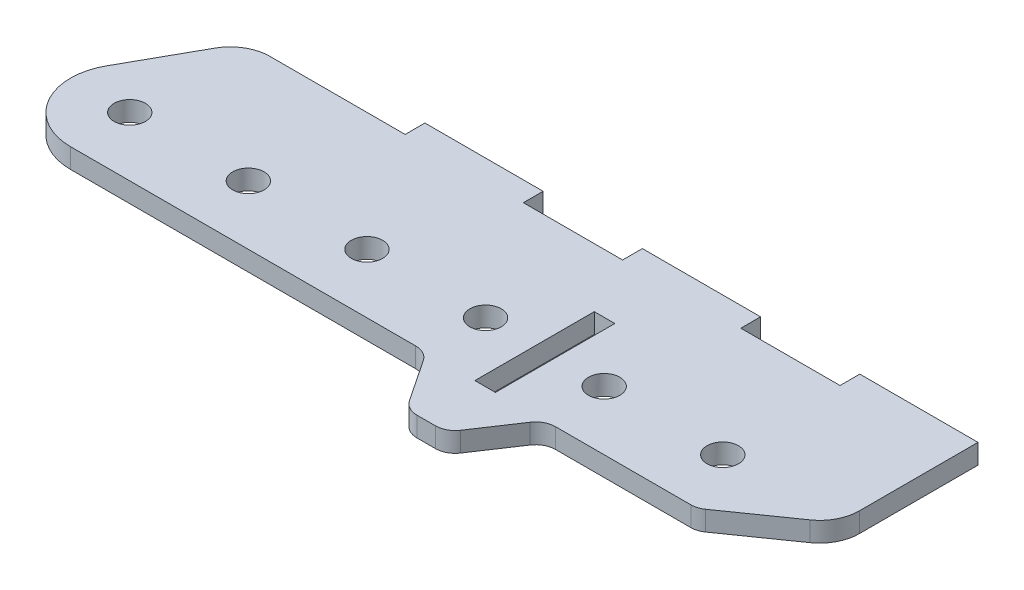
SolidWorks part; units mm, degrees
material "Plain Carbon Steel"
ref_plane "Front Plane" through (0, 0, 0) normal (0, 0, 1) x (1, 0, 0)
ref_plane "Top Plane" through (0, 0, 0) normal (0, 1, 0) x (1, 0, 0)
ref_plane "Right Plane" through (0, 0, 0) normal (1, 0, 0) x (0, 0, -1)
sketch "Sketch1" plane through (0, 0, 0) normal (0, 1, 0) x (1, 0, 0)
  line L1 (0, 0) -> (-304.8, 0)
  line L2 (0, 0) -> (0, -76.2)
  line L3 (0, -76.2) -> (-304.8, -76.2)
  line L4 (-304.8, 0) -> (-304.8, -76.2)
  dimension "D1" = 76.2
  dimension "D2" = 304.8
extrude "Boss-Extrude1" add sketch "Sketch1" along normal blind 6.35
chamfer "Chamfer1" distance 53.975 angle 35 1 edges at (0, 3.175, 76.2)
sketch "Sketch2" plane through (0, 6.35, 0) normal (0, 1, 0) x (1, 0, 0)
  line L0 (0, 0) -> (0, 6.35)
  line L1 (0, 6.35) -> (-37.973, 6.35)
  line L3 (-37.973, 6.35) -> (-37.973, 0)
  line L4 (0, 0) -> (-304.8, 0) construction
  line L5 (-37.973, 0) -> (0, 0)
  dimension "D1" = 37.973
  dimension "D2" = 6.35
extrude "Boss-Extrude2" add sketch "Sketch2" against normal blind 6.35
pattern_linear "LPattern1" count 3 spacing 69.85 along (-1, 0, 0) of "Boss-Extrude2"
hole_wizard "3/8 Clearance Hole1" positions "Sketch4" profile "Sketch5" hole size "3/8" standard "ANSI Inch" end condition through all
sketch "Sketch4" plane through (0, 6.35, 0) normal (0, 1, 0) x (1, 0, 0)
  point P0 (-37.5406, -38.1)
  point P3 (-75.6406, -38.1)
  point P6 (-113.7406, -38.1)
  point P9 (-151.8406, -38.1)
  point P12 (-189.9406, -38.1)
  point P15 (-228.0406, -38.1)
sketch "Sketch5" plane through (-37.5406, 6.35, 38.1) normal (1, 0, 0) x (0, 0, 1)
  line L0 (0, 0) -> (0, 6.35)
  line L1 (0, 6.35) -> (5.0419, 6.35)
  line L2 (5.0419, 6.35) -> (5.0419, 0)
  line L5 (5.0419, 0) -> (0, 0)
  line L11 (0, -6.35) -> (0, 107.95) construction
  dimension "Thru Hole Dia." = 10.0838
  dimension "Thru Hole Depth" = 6.35
sketch "Sketch6" plane through (0, 6.35, 0) normal (0, 1, 0) x (1, 0, 0)
  line L0 (-228.6, 0) -> (-304.8, 0)
  line L1 (-177.673, 0) -> (-304.8, 0) construction
  line L2 (-228.6, 0) -> (-228.6, 9.525) construction
  line L3 (-304.8, 0) -> (-304.8, -76.2)
  line L4 (-304.8, -76.2) -> (-228.6, -76.2)
  line L5 (-304.8, -76.2) -> (-53.975, -76.2) construction
  line L6 (-228.6, -76.2) -> (-228.6, 0)
  line L7 (-228.6, 0) -> (-244.677, -28.8193)
  line L8 (-228.6, -76.2) -> (-244.677, -47.3807)
  circle A0 centre (-228.0406, -38.1) radius 19.05
  line M7 (-304.8, -76.2) -> (-53.975, -76.2)
  line M20 (-177.673, 0) -> (-304.8, 0)
  line M21 (-304.8, 0) -> (-304.8, -76.2)
  dimension "D1" = 38.1
extrude "Cut-Extrude1" cut sketch "Sketch6" against normal through all contours A0 L7 L8 M20 M21 M7
fillet "Fillet1" radius 12.7 4 edges at (-228.6, 3.175, 76.2) (-53.975, 3.175, 76.2) (0, 3.175, 38.4063) (-228.6, 3.175, 0)
sketch "Sketch7" plane through (0, 6.35, 0) normal (0, 1, 0) x (1, 0, 0)
  line L0 (-113.7406, -38.1) -> (-75.6406, -38.1) construction
  line L1 (-94.6906, -38.1) -> (-94.6906, -18.923) construction
  line L2 (-97.9926, -18.923) -> (-91.3886, -18.923)
  line L3 (-97.9926, -18.923) -> (-97.9926, -57.277)
  line L4 (-97.9926, -57.277) -> (-91.3886, -57.277)
  line L5 (-91.3886, -18.923) -> (-91.3886, -57.277)
  line L6 (-94.6906, -38.1) -> (-94.6906, -57.277) construction
  dimension "D1" = 38.354
  dimension "D2" = 6.604
extrude "Cut-Extrude2" cut sketch "Sketch7" against normal through all
sketch "Sketch8" plane through (0, 6.35, 0) normal (0, 1, 0) x (1, 0, 0)
  line L0 (-228.0406, -57.15) -> (-113.7406, -57.15)
  line L1 (-113.7406, -57.15) -> (-101.0406, -76.2)
  line L2 (-221.1423, -76.2) -> (-57.9793, -76.2) construction
  line L3 (-101.0406, -76.2) -> (-88.3406, -76.2)
  line L4 (-88.3406, -76.2) -> (-75.6406, -57.15)
  line L5 (-75.6406, -57.15) -> (-26.7688, -57.15)
  line L6 (-50.6949, -73.9032) -> (-5.4156, -42.1983) construction
  line L7 (-94.6906, -57.277) -> (-94.6906, -76.2) construction
  line L8 (-97.9926, -57.277) -> (-91.3886, -57.277) construction
  line L9 (-247.0906, -38.1) -> (-247.0906, -76.2)
  line L10 (-247.0906, -76.2) -> (-26.7688, -76.2)
  line L11 (-26.7688, -76.2) -> (-26.7688, -57.15)
  circle A0 centre (-228.0406, -38.1) radius 19.05
  circle A1 centre (-113.7406, -38.1) radius 19.05
  circle A2 centre (-75.6406, -38.1) radius 19.05
  arc A3 (-244.677, -28.8193) -> (-244.677, -47.3807) centre (-228.0406, -38.1) ccw construction
  line M5 (-244.677, -47.3807) -> (-232.2332, -69.6872)
  arc M6 (-232.2332, -69.6872) -> (-221.1423, -76.2) centre (-221.1423, -63.5) ccw
  line M7 (-221.1423, -76.2) -> (-57.9793, -76.2)
  arc M8 (-57.9793, -76.2) -> (-50.6949, -73.9032) centre (-57.9793, -63.5) ccw
  line M9 (-50.6949, -73.9032) -> (-5.4156, -42.1983)
  dimension "D1" = 12.7
extrude "Cut-Extrude3" cut sketch "Sketch8" against normal through all contours A0 L1 L0 M5 M6 M7 | L5 L4 M7 M8 M9
fillet "Fillet2" radius 6.35 5 edges at (-113.7406, 3.175, 57.15) (-26.7688, 3.175, 57.15) (-75.6406, 3.175, 57.15) (-88.3406, 3.175, 76.2) (-101.0406, 3.175, 76.2)
